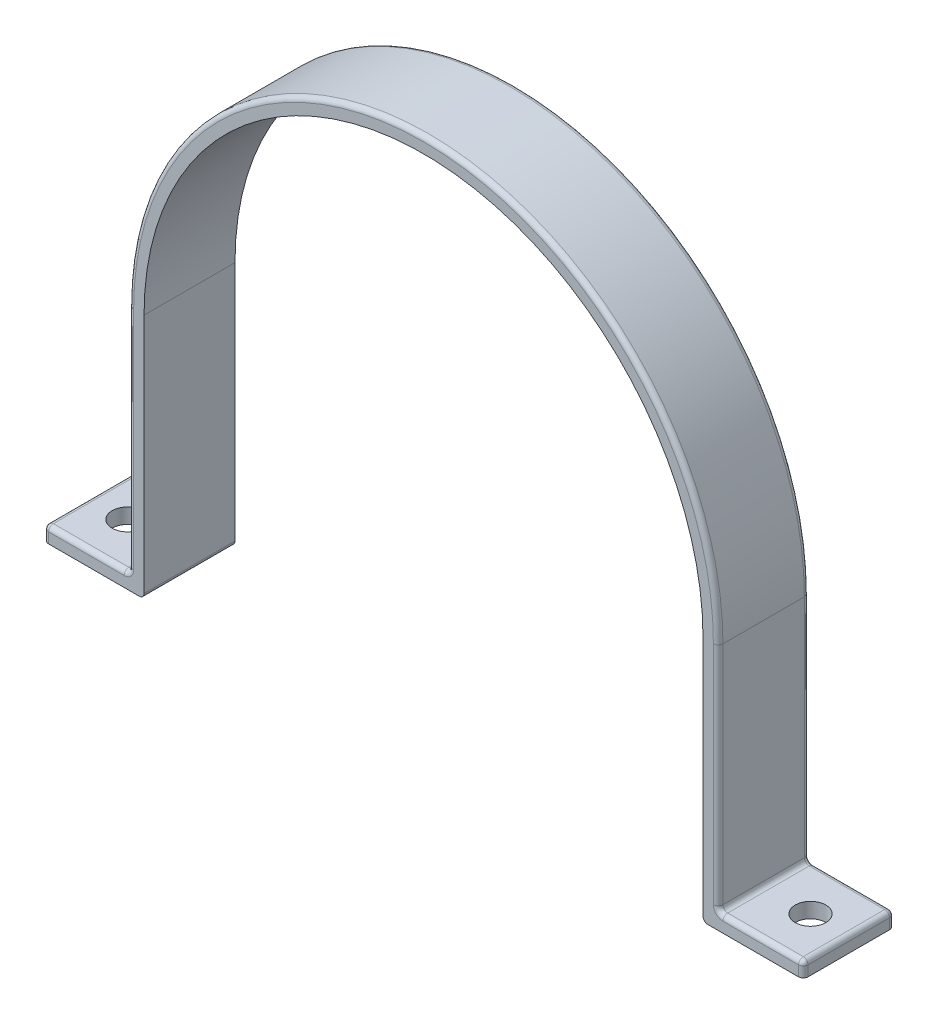
SolidWorks part; units mm, degrees
material "6061-T6 (SS)"
ref_plane "Front Plane" through (0, 0, 0) normal (0, 0, 1) x (1, 0, 0)
ref_plane "Top Plane" through (0, 0, 0) normal (0, 1, 0) x (1, 0, 0)
ref_plane "Right Plane" through (0, 0, 0) normal (1, 0, 0) x (0, 0, -1)
sketch "Sketch1" plane through (0, 0, 0) normal (0, 0, 1) x (1, 0, 0)
  line L0 (21, 51.5) -> (21, 0)
  line L2 (21, 0) -> (0, 0)
  line L3 (138.09, 51.5) -> (138.09, 0)
  line L4 (138.09, 0) -> (159.09, 0)
  line L5 (21, 51.5) -> (79.545, 51.5) construction
  line L6 (79.545, 51.5) -> (138.09, 51.5) construction
  line L7 (17.825, 3.175) -> (0, 3.175)
  line L8 (17.825, 51.5) -> (17.825, 3.175)
  line L9 (141.265, 51.5) -> (141.265, 3.175)
  line L10 (141.265, 3.175) -> (159.09, 3.175)
  line L11 (0, 3.175) -> (0, 0)
  line L12 (159.09, 0) -> (159.09, 3.175)
  arc A0 (138.09, 51.5) -> (21, 51.5) centre (79.545, 51.5) ccw
  arc A2 (141.265, 51.5) -> (17.825, 51.5) centre (79.545, 51.5) ccw
  dimension "D3" = 58.545
  dimension "D4" = 51.5
  dimension "D1" = 21
  dimension "D2" = 3.175
extrude "Boss-Extrude1" add sketch "Sketch1" against normal blind 19.05
sketch "Sketch2" plane through (0, 3.175, 0) normal (0, 1, 0) x (1, 0, 0)
  line L0 (151.09, 9.525) -> (151.09, 19.05) construction
  line L1 (0, 19.05) -> (0, 0) construction
  line L2 (159.09, 19.05) -> (159.09, 0) construction
  line L3 (159.09, 19.05) -> (141.265, 19.05) construction
  line L4 (151.09, 9.525) -> (151.09, 0) construction
  line L5 (159.09, 0) -> (141.265, 0) construction
  circle A0 centre (151.09, 9.525) radius 3.2
  circle A1 centre (8, 9.525) radius 3.2
  dimension "D3" = 6.4
  dimension "D1" = 8
  dimension "D2" = 8
extrude "Cut-Extrude1" cut sketch "Sketch2" against normal up to next
fillet "Fillet1" radius 1 20 edges at (138.09, 0, -9.525) (159.09, 3.175, -9.525) (141.265, 3.175, -9.525) (21, 0, -9.525) (17.825, 3.175, -9.525) (0, 3.175, -9.525) (141.265, 27.3375, 0) (79.545, 113.22, 0) (141.265, 27.3375, -19.05) (79.545, 113.22, -19.05) (159.09, 1.5875, -19.05) (159.09, 1.5875, 0) (150.1775, 3.175, -19.05) (150.1775, 3.175, 0) (17.825, 27.3375, 0) (17.825, 27.3375, -19.05) (0, 1.5875, -19.05) (8.9125, 3.175, -19.05) (8.9125, 3.175, 0) (0, 1.5875, 0)
equation "\"D2@Sketch2\"=\"D1@Sketch2\""
